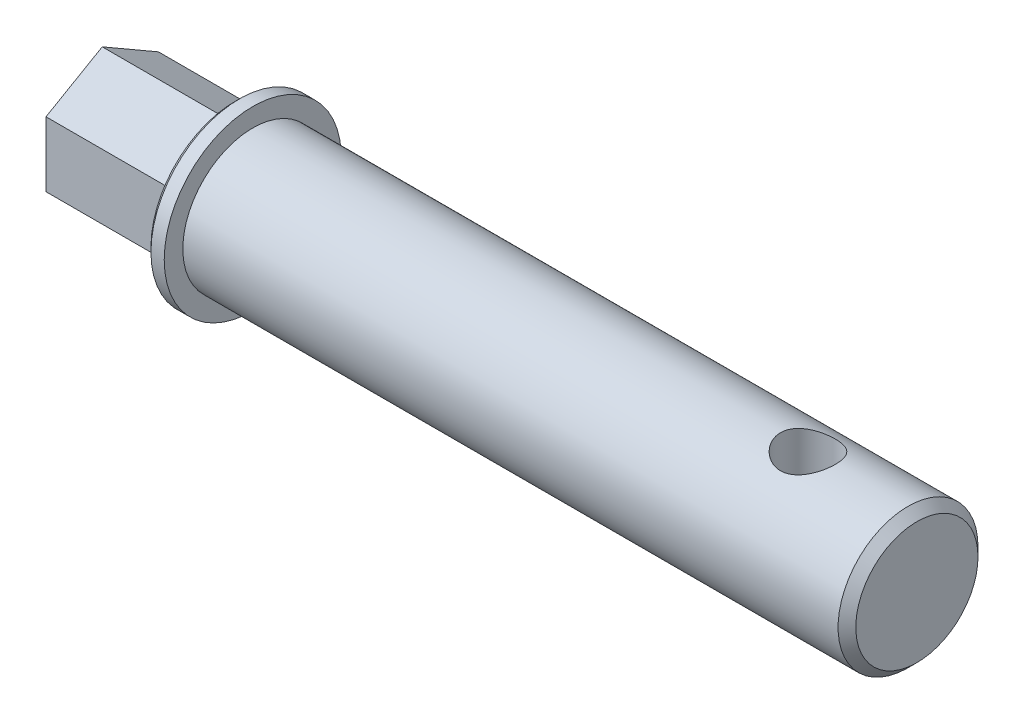
SolidWorks part; units mm, degrees
ref_plane "前视基准面" through (0, 0, 0) normal (0, 0, 1) x (1, 0, 0)
ref_plane "上视基准面" through (0, 0, 0) normal (0, 1, 0) x (1, 0, 0)
ref_plane "右视基准面" through (0, 0, 0) normal (1, 0, 0) x (0, 0, -1)
sketch "草图1" plane through (0, 0, 0) normal (1, 0, 0) x (0, 0, -1)
  circle A0 centre (0, 0) radius 7.9
extrude "凸台-拉伸1" add sketch "草图1" along normal blind 75
sketch "草图3" plane through (0, 0, 0) normal (-1, 0, 0) x (0, 0, 1)
  circle A0 centre (0, 0) radius 10
extrude "凸台-拉伸2" add sketch "草图3" along normal blind 2
sketch "草图4" plane through (-2, 0, 0) normal (-1, 0, 0) x (0, 0, 1)
  line L0 (0, 0) -> (0, 5) construction
  line L1 (6.35, 3.6662) -> (0, 7.3323)
  line L2 (0, 7.3323) -> (-6.35, 3.6662)
  line L3 (-6.35, 3.6662) -> (-6.35, -3.6662)
  line L4 (-6.35, -3.6662) -> (0, -7.3323)
  line L5 (0, -7.3323) -> (6.35, -3.6662)
  line L6 (6.35, -3.6662) -> (6.35, 3.6662)
  circle A0 centre (0, 0) radius 6.35 construction
  dimension "D1" = 12.7
  dimension "D2" = 60
extrude "凸台-拉伸3" add sketch "草图4" along normal blind 15
sketch "草图5" plane through (0, 0, 0) normal (0, 1, 0) x (1, 0, 0)
  circle A0 centre (62.7, 0) radius 3.1
  dimension "D1" = 6.2
  dimension "D2" = 62.7
chamfer "倒角1" distance 0.5 angle 45 1 edges at (-2, 0, 10)
hole_wizard "M5x0.8 螺纹孔1" positions "草图6" profile "草图7" tap size "M5x0.8" standard "ANSI Metric"
sketch "草图6" plane through (-17, 0, 0) normal (-1, 0, 0) x (0, 0, 1)
  point P0 (0, 0)
sketch "草图7" plane through (-17, 0, 0) normal (0, 1, 0) x (0, 0, 1)
  line L0 (0, 0) -> (0, 13.6618)
  line L1 (0, 13.6618) -> (2.1, 12.4)
  line L2 (2.1, 12.4) -> (2.1, 0)
  line L5 (2.1, 0) -> (0, 0)
  line L10 (0, 13.6618) -> (-2.1, 12.4) construction
  line L11 (0, -6.35) -> (0, 107.95) construction
  dimension "螺纹孔钻头直径" = 4.2
  dimension "螺纹孔钻头深度" = 12.4
  dimension "导头角度" = 118
cosmetic thread "孔螺蚊线1" parameters "D1"=10, "D2"=5
sketch3d "3D草图1"
  circle A0 centre (62.7, 7.9, 0) radius 3.1
  point P2 (62.7, 11, 0)
  dimension "D1" = 7.9
extrude "切除-拉伸1" cut sketch "草图5" against normal through all both and the other way through all
chamfer "倒角2" distance 1 angle 45 1 edges at (75, 0, -7.9)
